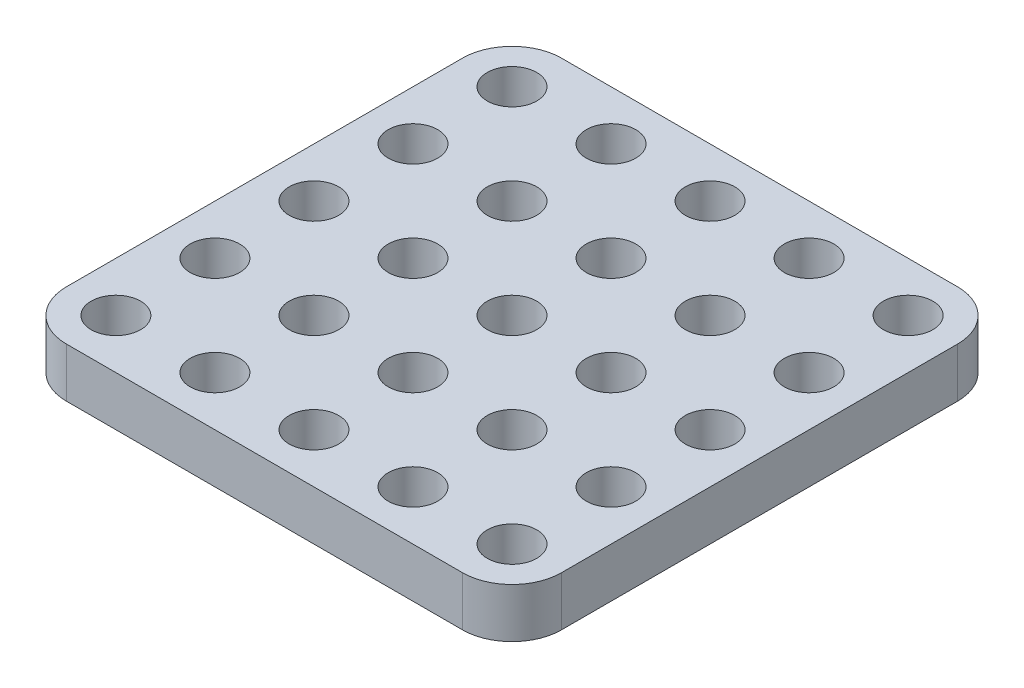
SolidWorks part; units mm, degrees
ref_plane "Front Plane" through (0, 0, 0) normal (0, 0, 1) x (1, 0, 0)
ref_plane "Top Plane" through (0, 0, 0) normal (0, 1, 0) x (1, 0, 0)
ref_plane "Right Plane" through (0, 0, 0) normal (1, 0, 0) x (0, 0, -1)
sketch "Sketch1" plane through (0, 0, 0) normal (0, 1, 0) x (1, 0, 0)
  line L1 (20, -25) -> (-20, -25)
  line L2 (25, -20) -> (25, 20)
  line L3 (20, 25) -> (-20, 25)
  line L4 (-25, -20) -> (-25, 20)
  line L5 (25, -25) -> (-25, 25) construction
  line L6 (25, 25) -> (-25, -25) construction
  arc A0 (20, 25) -> (25, 20) centre (20, 20) cw
  arc A1 (25, -20) -> (20, -25) centre (20, -20) cw
  arc A2 (-20, -25) -> (-25, -20) centre (-20, -20) cw
  arc A3 (-25, 20) -> (-20, 25) centre (-20, 20) cw
  circle A4 centre (-20, 20) radius 2.5
  circle A5 centre (-10, 20) radius 2.5
  circle A6 centre (0, 20) radius 2.5
  circle A7 centre (10, 20) radius 2.5
  circle A8 centre (20, 20) radius 2.5
  circle A14 centre (-10, 10) radius 2.5
  circle A15 centre (0, 10) radius 2.5
  circle A16 centre (10, 10) radius 2.5
  circle A17 centre (20, 10) radius 2.5
  circle A23 centre (-10, 0) radius 2.5
  circle A24 centre (0, 0) radius 2.5
  circle A25 centre (10, 0) radius 2.5
  circle A26 centre (20, 0) radius 2.5
  circle A32 centre (-10, -10) radius 2.5
  circle A33 centre (0, -10) radius 2.5
  circle A34 centre (10, -10) radius 2.5
  circle A35 centre (20, -10) radius 2.5
  circle A41 centre (-10, -20) radius 2.5
  circle A42 centre (0, -20) radius 2.5
  circle A43 centre (10, -20) radius 2.5
  circle A44 centre (20, -20) radius 2.5
  circle A68 centre (-20, 10) radius 2.5
  circle A69 centre (-20, 0) radius 2.5
  circle A70 centre (-20, -10) radius 2.5
  circle A71 centre (-20, -20) radius 2.5
  circle A74 centre (40, 20) radius 2.5 [skipped]
  circle A75 centre (50, 20) radius 2.5 [skipped]
  circle A76 centre (60, 20) radius 2.5 [skipped]
  circle A77 centre (70, 20) radius 2.5 [skipped]
  circle A78 centre (30, 10) radius 2.5 [skipped]
  circle A79 centre (40, 10) radius 2.5 [skipped]
  circle A80 centre (50, 10) radius 2.5 [skipped]
  circle A81 centre (60, 10) radius 2.5 [skipped]
  circle A82 centre (70, 10) radius 2.5 [skipped]
  circle A83 centre (40, 0) radius 2.5 [skipped]
  circle A84 centre (50, 0) radius 2.5 [skipped]
  circle A85 centre (60, 0) radius 2.5 [skipped]
  circle A86 centre (70, 0) radius 2.5 [skipped]
  circle A87 centre (40, -10) radius 2.5 [skipped]
  circle A88 centre (50, -10) radius 2.5 [skipped]
  circle A89 centre (60, -10) radius 2.5 [skipped]
  circle A90 centre (70, -10) radius 2.5 [skipped]
  circle A91 centre (50, -20) radius 2.5 [skipped]
  circle A92 centre (60, -20) radius 2.5 [skipped]
  circle A93 centre (70, -20) radius 2.5 [skipped]
  circle A94 centre (60, -30) radius 2.5 [skipped]
  circle A95 centre (70, -30) radius 2.5 [skipped]
  circle A96 centre (70, -40) radius 2.5 [skipped]
  circle A97 centre (30, 20) radius 2.5 [skipped]
  circle A98 centre (-10, -40) radius 2.5 [skipped]
  circle A99 centre (-20, -40) radius 2.5 [skipped]
  circle A100 centre (-20, -30) radius 2.5 [skipped]
  circle A101 centre (0, -40) radius 2.5 [skipped]
  circle A102 centre (10, -40) radius 2.5 [skipped]
  circle A103 centre (-10, -30) radius 2.5 [skipped]
  circle A104 centre (0, -30) radius 2.5 [skipped]
  circle A105 centre (10, -30) radius 2.5 [skipped]
  circle A106 centre (20, -30) radius 2.5 [skipped]
  circle A107 centre (30, -30) radius 2.5 [skipped]
  circle A108 centre (40, -30) radius 2.5 [skipped]
  circle A109 centre (50, -30) radius 2.5 [skipped]
  circle A110 centre (20, -40) radius 2.5 [skipped]
  circle A111 centre (30, -40) radius 2.5 [skipped]
  circle A112 centre (40, -40) radius 2.5 [skipped]
  circle A113 centre (50, -40) radius 2.5 [skipped]
  circle A114 centre (60, -40) radius 2.5 [skipped]
  circle A115 centre (40, -20) radius 2.5 [skipped]
  circle A116 centre (30, 0) radius 2.5 [skipped]
  circle A117 centre (30, -10) radius 2.5 [skipped]
  circle A118 centre (30, -20) radius 2.5 [skipped]
  point P0 (0, 0)
  dimension "D3" = 5
  dimension "D4" = 5
  dimension "D1" = 50
  dimension "D5" = 7
extrude "Boss-Extrude1" add sketch "Sketch1" along normal blind 5
